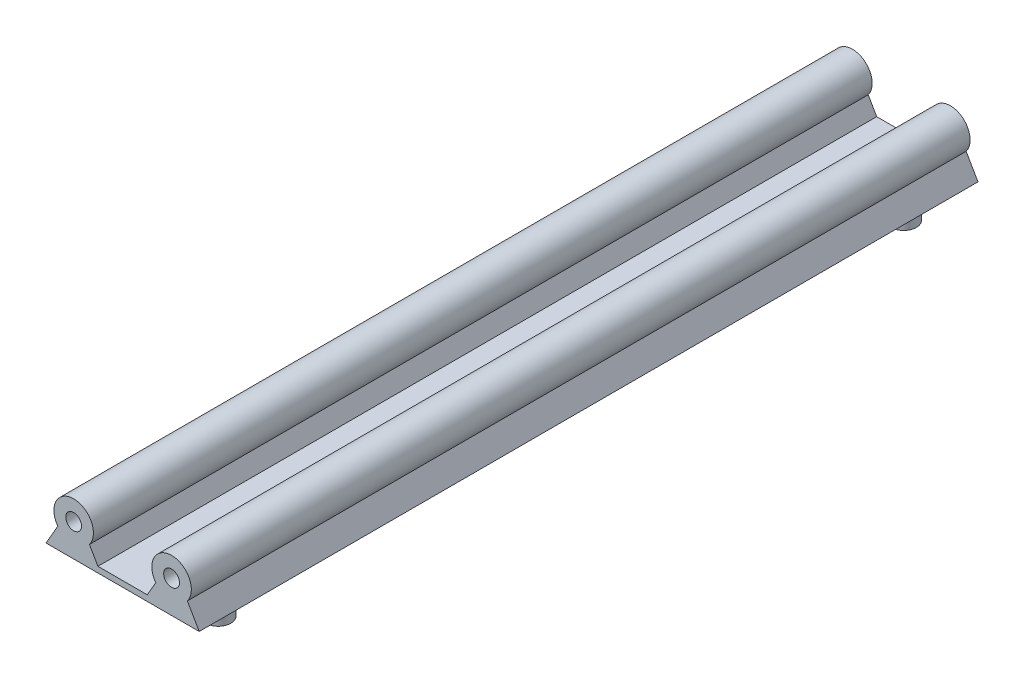
SolidWorks part; units mm, degrees
ref_plane "Front Plane" through (0, 0, 0) normal (0, 0, 1) x (1, 0, 0)
ref_plane "Top Plane" through (0, 0, 0) normal (0, 1, 0) x (1, 0, 0)
ref_plane "Right Plane" through (0, 0, 0) normal (1, 0, 0) x (0, 0, -1)
sketch "Sketch1" plane through (0, 0, 0) normal (0, 0, 1) x (1, 0, 0)
  line L0 (-4, -3) -> (4, -3) construction
  line L1 (-4, -3) -> (-7, -8.1962)
  line L2 (4, -3) -> (7, -8.1962)
  line L3 (-7, -8.1962) -> (7, -8.1962)
  line L4 (28.8, -3) -> (31.8, -8.1962)
  line L5 (17.8, -8.1962) -> (31.8, -8.1962)
  line L6 (20.8, -3) -> (17.8, -8.1962)
  circle A0 centre (0, 0) radius 5
  arc A1 (-4, -3) -> (4, -3) centre (0, 0) cw
  arc A2 (20.8, -3) -> (28.8, -3) centre (24.8, 0) cw
  dimension "D1" = 3
  dimension "D2" = 2
  dimension "D3" = 8
extrude "Boss-Extrude1" add sketch "Sketch1" along normal blind 220 contours A0 L0 | L0 A0 | A0 L1 L3 L2 | L4 L5 L6 A2
sketch "Sketch3" plane through (0, 0, 220) normal (0, 0, 1) x (1, 0, 0)
  line L0 (7, -8.1962) -> (17.8, -8.1962)
  line L1 (6.15, -6.7239) -> (18.65, -6.7239)
  line L2 (4, -3) -> (7, -8.1962) construction
  line L3 (20.8, -3) -> (17.8, -8.1962) construction
  line L4 (18.65, -6.7239) -> (18.65, -8.1962)
  line L5 (17.8, -8.1962) -> (31.8, -8.1962) construction
  line L6 (18.65, -8.1962) -> (17.8, -8.1962)
  line L7 (6.15, -6.7239) -> (6.15, -8.1962)
  line L8 (-7, -8.1962) -> (7, -8.1962) construction
  line L9 (6.15, -8.1962) -> (7, -8.1962)
  dimension "D1" = 12.5
sketch "Sketch4" plane through (0, -8.1962, 0) normal (0, -1, 0) x (1, 0, 0)
  line L0 (24.8, 220) -> (24.8, 0) construction
  line L1 (17.8, 220) -> (31.8, 220) construction
  line L2 (17.8, 0) -> (31.8, 0) construction
  line L3 (0, 0) -> (0, 220) construction
  line L4 (-7, 220) -> (7, 220) construction
  circle A0 centre (0, 196.8) radius 3.2
  circle A1 centre (24.8, 196.8) radius 3.2
  circle A2 centre (24.8, 172) radius 3.2
  circle A3 centre (24.8, 147.2) radius 3.2
  circle A4 centre (24.8, 122.4) radius 3.2
  circle A5 centre (24.8, 97.6) radius 3.2
  circle A6 centre (24.8, 72.8) radius 3.2
  circle A7 centre (24.8, 48) radius 3.2
  circle A8 centre (24.8, 23.2) radius 3.2
  circle A9 centre (0, 172) radius 3.2
  circle A10 centre (0, 147.2) radius 3.2
  circle A11 centre (0, 122.4) radius 3.2
  circle A12 centre (0, 97.6) radius 3.2
  circle A13 centre (0, 72.8) radius 3.2
  circle A14 centre (0, 48) radius 3.2
  circle A15 centre (0, 23.2) radius 3.2
  dimension "D1" = 2
  dimension "D3" = 23.2
  dimension "D2" = 8
extrude "Boss-Extrude3" add sketch "Sketch4" along normal blind 6
extrude "Boss-Extrude4" add sketch "Sketch3" against normal blind 220
sketch "Sketch5" plane through (0, 0, 0) normal (0, 0, -1) x (-1, 0, 0)
  circle A0 centre (0, 0) radius 1.37
  circle A1 centre (-24.8, 0) radius 1.37
  dimension "D1" = 2
extrude "Cut-Extrude1" cut sketch "Sketch5" against normal blind 7
sketch "Sketch6" plane through (0, 0, 220) normal (0, 0, 1) x (1, 0, 0)
  circle A0 centre (0, 0) radius 1.37
  circle A1 centre (24.8, 0) radius 1.37
  dimension "D1" = 2
extrude "Cut-Extrude2" cut sketch "Sketch6" against normal blind 7
sketch "Sketch7" plane through (0, -14.1962, 0) normal (0, -1, 0) x (1, 0, 0)
  circle A0 centre (0, 172) radius 3.2
  circle A1 centre (24.8, 172) radius 3.2
  circle A2 centre (24.8, 147.2) radius 3.2
  circle A3 centre (24.8, 122.4) radius 3.2
  circle A4 centre (24.8, 97.6) radius 3.2
  circle A5 centre (24.8, 72.8) radius 3.2
  circle A6 centre (24.8, 48) radius 3.2
  circle A7 centre (0, 147.2) radius 3.2
  circle A8 centre (0, 122.4) radius 3.2
  circle A9 centre (0, 97.6) radius 3.2
  circle A10 centre (0, 72.8) radius 3.2
  circle A11 centre (0, 48) radius 3.2
  dimension "D1" = 2
  dimension "D2" = 6
extrude "Cut-Extrude3" cut sketch "Sketch7" against normal blind 6
sketch "Sketch9" plane through (0, 0, 0) normal (0, 0, -1) x (-1, 0, 0)
  line L0 (4, -3) -> (7, -8.1962) construction
  line L1 (-4, -3) -> (-6.15, -6.7239) construction
  line L2 (-18.65, -6.7239) -> (-6.15, -6.7239) construction
  line L3 (-20.8, -3) -> (-18.65, -6.7239) construction
  line L4 (7, -8.1962) -> (-31.8, -8.1962) construction
  line L5 (-28.8, -3) -> (-31.8, -8.1962) construction
  line L6 (4, -3) -> (7, -8.1962)
  line L7 (-4, -3) -> (-6.15, -6.7239)
  line L8 (-18.65, -6.7239) -> (-6.15, -6.7239)
  line L9 (-20.8, -3) -> (-18.65, -6.7239)
  line L10 (7, -8.1962) -> (-31.8, -8.1962)
  line L11 (-28.8, -3) -> (-31.8, -8.1962)
  arc A0 (4, -3) -> (-4, -3) centre (0, 0) ccw construction
  arc A1 (-20.8, -3) -> (-28.8, -3) centre (-24.8, 0) ccw construction
  arc A2 (4, -3) -> (-4, -3) centre (0, 0) ccw
  arc A3 (-20.8, -3) -> (-28.8, -3) centre (-24.8, 0) ccw
extrude "Cut-Extrude4" cut sketch "Sketch9" against normal blind 11.4
sketch "Sketch10" plane through (0, 0, 11.4) normal (0, 0, -1) x (-1, 0, 0)
  circle A1 centre (-24.8, 0) radius 2
  circle A2 centre (0, 0) radius 2
extrude "Cut-Extrude5" cut sketch "Sketch10" against normal blind 7
sketch "Sketch11" plane through (0, 0, 220) normal (0, 0, 1) x (1, 0, 0)
  line L6 (20.8, -3) -> (18.65, -6.7239)
  line L7 (18.65, -6.7239) -> (6.15, -6.7239)
  line L8 (6.15, -6.7239) -> (4, -3)
  line L9 (-4, -3) -> (-7, -8.1962)
  line L10 (-7, -8.1962) -> (31.8, -8.1962)
  line L11 (31.8, -8.1962) -> (28.8, -3)
  line L12 (20.8, -3) -> (18.65, -6.7239)
  line L13 (18.65, -6.7239) -> (6.15, -6.7239)
  line L14 (6.15, -6.7239) -> (4, -3)
  line L15 (-4, -3) -> (-7, -8.1962)
  line L16 (-7, -8.1962) -> (31.8, -8.1962)
  line L17 (31.8, -8.1962) -> (28.8, -3)
  arc A2 (4, -3) -> (-4, -3) centre (0, 0) ccw
  arc A3 (28.8, -3) -> (20.8, -3) centre (24.8, 0) ccw
  arc A4 (4, -3) -> (-4, -3) centre (0, 0) ccw
  arc A5 (28.8, -3) -> (20.8, -3) centre (24.8, 0) ccw
  dimension "D1" = 0
extrude "Cut-Extrude6" cut sketch "Sketch11" against normal blind 11.4
sketch "Sketch12" plane through (0, 0, 208.6) normal (0, 0, 1) x (1, 0, 0)
  line L0 (19.8, 0) -> (29.8, 0) construction
  circle A0 centre (0, 0) radius 2
  arc A1 (28.8, -3) -> (20.8, -3) centre (24.8, 0) ccw construction
  circle A2 centre (24.8, 0) radius 2
extrude "Cut-Extrude7" cut sketch "Sketch12" against normal blind 7
